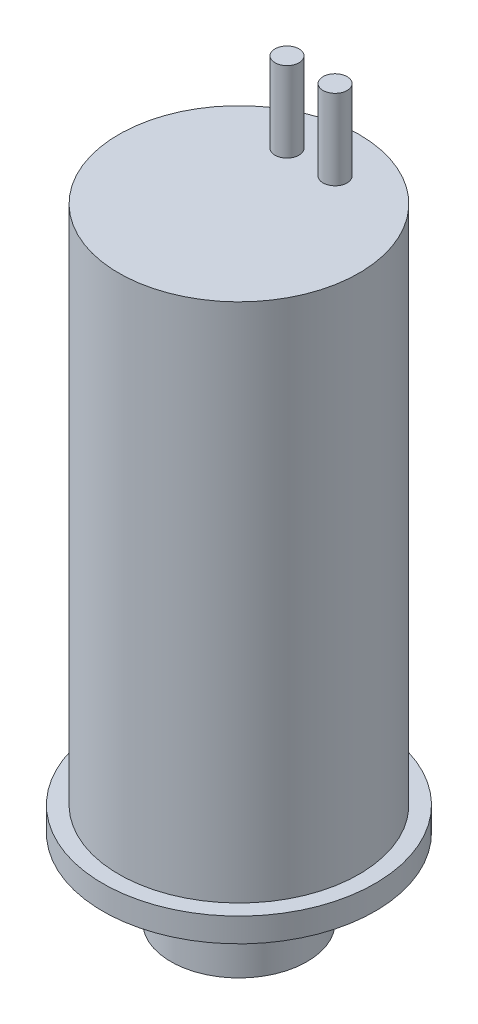
SolidWorks part; units mm, degrees
ref_plane "Front Plane" through (0, 0, 0) normal (0, 0, 1) x (1, 0, 0)
ref_plane "Top Plane" through (0, 0, 0) normal (0, 1, 0) x (1, 0, 0)
ref_plane "Right Plane" through (0, 0, 0) normal (1, 0, 0) x (0, 0, -1)
sketch "Sketch1" plane through (0, 0, 0) normal (0, 0, 1) x (1, 0, 0)
  line L0 (0, 0) -> (-4.25, 0)
  line L1 (-4.25, 0) -> (-4.25, 5.5)
  line L2 (-4.25, 5.5) -> (-8.5, 5.5)
  line L3 (-8.5, 5.5) -> (-8.5, 7)
  line L4 (-8.5, 7) -> (-7.5, 7)
  line L5 (-7.5, 7) -> (-7.5, 39.5)
  line L6 (-7.5, 39.5) -> (0, 39.5)
  line L7 (0, 0) -> (0, 39.5)
  line L8 (7.5, 39.5) -> (0, 39.5) construction
  line L9 (7.5, 7) -> (7.5, 39.5) construction
  line L10 (8.5, 7) -> (7.5, 7) construction
  line L11 (8.5, 5.5) -> (8.5, 7) construction
  line L12 (4.25, 5.5) -> (8.5, 5.5) construction
  line L13 (4.25, 0) -> (4.25, 5.5) construction
  line L14 (0, 0) -> (4.25, 0) construction
  point P15 (-8.5, 6.25)
  dimension "D1" = 8.5
  dimension "D2" = 17
  dimension "D3" = 15
  dimension "D4" = 32.5
  dimension "D5" = 34
  dimension "D6" = 39.5
revolve "Revolve2" add sketch "Sketch1" angle 360 about L7
sketch "Sketch2" plane through (0, 39.5, 0) normal (0, 1, 0) x (1, 0, 0)
  line L0 (0, -7.5) -> (0, 7.5) construction
  circle A0 centre (0, 0) radius 7.5 construction
  circle A1 centre (0, 0) radius 7.5 construction
  circle A2 centre (1.5, 4.5) radius 0.75
  circle A3 centre (-1.5, 4.5) radius 0.75
  dimension "D3" = 1.5
  dimension "D1" = 3
  dimension "D2" = 3
extrude "Boss-Extrude1" add sketch "Sketch2" along normal blind 5
sketch "Sketch3" plane through (0, 0, 0) normal (1, 0, 0) x (0, 0, -1)
  line L6 (0, 0) -> (0, 5.5) construction
  line L7 (-4.25, 5.5) -> (4.25, 5.5) construction
  line L8 (-4.25, 0) -> (4.25, 0) construction
  line L9 (4.25, 0) -> (3.26, 0)
  line L10 (4.25, 0) -> (4.25, 0.65)
  line L11 (4.25, 0.65) -> (3.26, 0.65)
  line L12 (3.26, 0) -> (3.26, 0.65)
  line L13 (4.25, 0) -> (4.25, 5.5) construction
  dimension "D1" = 0.65
  dimension "D2" = 6.52
revolve "Cut-Revolve1" cut sketch "Sketch3" angle 360 about L6
sketch "Sketch4" plane through (0, 0, 0) normal (0, -1, 0) x (1, 0, 0)
  circle A0 centre (0, 0) radius 1.17
  dimension "D1" = 2.34
extrude "Cut-Extrude1" cut sketch "Sketch4" against normal blind 7.5
sketch "Sketch5" plane through (0, 0, 0) normal (1, 0, 0) x (0, 0, -1)
  line L0 (-8.5, 5.5) -> (8.5, 5.5) construction
  line L1 (7.63, 5.5) -> (6.5, 5.5)
  line L2 (7.63, 5.5) -> (7.63, 6.4)
  line L3 (7.63, 6.4) -> (6.5, 6.4)
  line L4 (6.5, 5.5) -> (6.5, 6.4)
  line L5 (0, 0) -> (0, 7) construction
  line L6 (8.5, 7) -> (-8.5, 7) construction
  point P11 (7.065, 5.5)
  dimension "D1" = 13
  dimension "D2" = 15.26
  dimension "D3" = 0.9
revolve "Cut-Revolve2" cut sketch "Sketch5" angle 360 about L5
